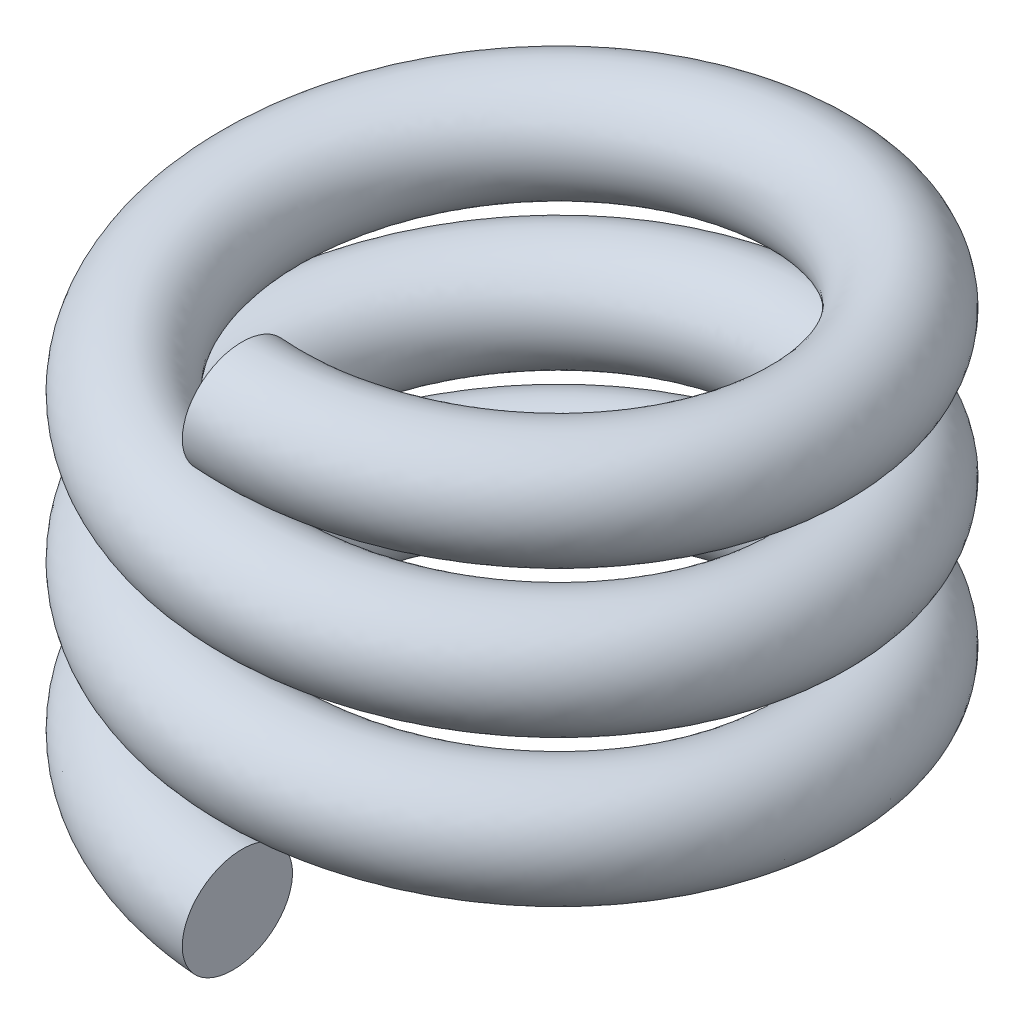
SolidWorks part; units mm, degrees
ref_plane "Front Plane" through (0, 0, 0) normal (0, 0, 1) x (1, 0, 0)
ref_plane "Top Plane" through (0, 0, 0) normal (0, 1, 0) x (1, 0, 0)
ref_plane "Right Plane" through (0, 0, 0) normal (1, 0, 0) x (0, 0, -1)
sketch "Sketch3" plane through (0, 0, 0) normal (0, 1, 0) x (1, 0, 0)
  circle A0 centre (0, 0) radius 25
  dimension "D1" = 50
curve "Helix/Spiral1" pitch 13.3333 height 40 turns 3
sweep "Sweep1" add path "Helix/Spiral1" circular profile diameter 10 parameters "D3"=10
